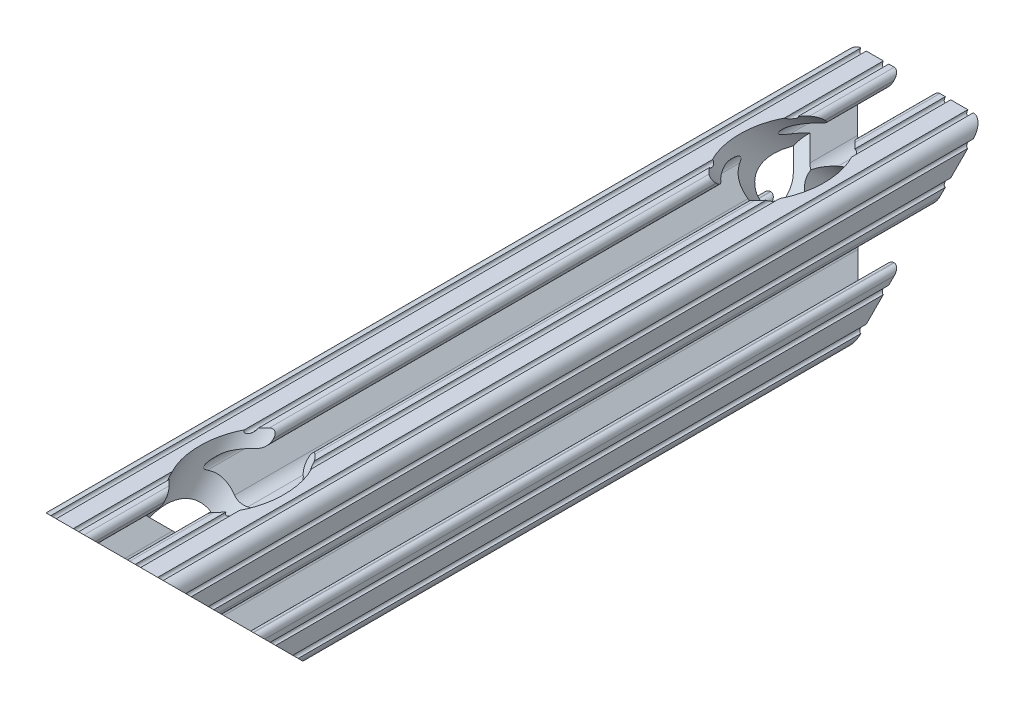
SolidWorks part; units mm, degrees
ref_plane "Front Plane" through (0, 0, 0) normal (0, 0, 1) x (1, 0, 0)
ref_plane "Top Plane" through (0, 0, 0) normal (0, 1, 0) x (1, 0, 0)
ref_plane "Right Plane" through (0, 0, 0) normal (1, 0, 0) x (0, 0, -1)
sketch "Sketch1" plane through (0, 0, 0) normal (0, 0, 1) x (1, 0, 0)
  line L2 (-7.1797, -8.6452) -> (-3.9523, -5.4237)
  line L3 (-1.7093, -4.4958) -> (1.7093, -4.4958)
  line L4 (3.9523, -5.4237) -> (7.1797, -8.6452)
  line L6 (6.4164, -10.4902) -> (4.2875, -10.4902)
  line L7 (3.2385, -11.5392) -> (3.2385, -11.651)
  line L8 (4.2875, -12.7) -> (5.3171, -12.7)
  line L9 (6.3331, -12.7) -> (9.5504, -12.7)
  line L10 (12.7, -9.5504) -> (12.7, -6.3331)
  line L11 (12.7, -5.3171) -> (12.7, -4.2875)
  line L12 (11.651, -3.2385) -> (11.5392, -3.2385)
  line L13 (10.4902, -4.2875) -> (10.4902, -6.4021)
  line L14 (8.7371, -7.1294) -> (5.441, -3.8408)
  line L15 (4.5085, -1.5932) -> (4.5085, 1.5932)
  line L16 (5.441, 3.8408) -> (8.7371, 7.1294)
  line L17 (10.4902, 6.4021) -> (10.4902, 4.2875)
  line L18 (11.5392, 3.2385) -> (11.651, 3.2385)
  line L19 (12.7, 4.2875) -> (12.7, 5.3171)
  line L20 (12.7, 6.3331) -> (12.7, 9.5504)
  line L21 (9.5504, 12.7) -> (6.3331, 12.7)
  line L22 (5.3171, 12.7) -> (4.2875, 12.7)
  line L23 (3.2385, 11.651) -> (3.2385, 11.5392)
  line L24 (4.2875, 10.4902) -> (6.4768, 10.4902)
  line L25 (7.207, 8.7244) -> (3.8983, 5.4232)
  line L26 (1.6558, 4.4958) -> (-1.6558, 4.4958)
  line L27 (-3.8983, 5.4232) -> (-7.207, 8.7244)
  line L28 (-6.4768, 10.4902) -> (-4.2875, 10.4902)
  line L29 (-3.2385, 11.5392) -> (-3.2385, 11.651)
  line L30 (-4.2875, 12.7) -> (-5.3171, 12.7)
  line L31 (-6.3331, 12.7) -> (-9.5504, 12.7)
  line L32 (-12.7, 9.5504) -> (-12.7, 6.3331)
  line L33 (-12.7, 5.3171) -> (-12.7, 4.2875)
  line L34 (-11.651, 3.2385) -> (-11.5392, 3.2385)
  line L35 (-10.4902, 4.2875) -> (-10.4902, 6.4021)
  line L36 (-8.7371, 7.1294) -> (-5.441, 3.8408)
  line L37 (-4.5085, 1.5932) -> (-4.5085, -1.5932)
  line L38 (-5.441, -3.8408) -> (-8.7371, -7.1294)
  line L39 (-10.4902, -6.4021) -> (-10.4902, -4.2875)
  line L40 (-11.5392, -3.2385) -> (-11.651, -3.2385)
  line L41 (-12.7, -4.2875) -> (-12.7, -5.3171)
  line L42 (-12.7, -6.3331) -> (-12.7, -9.5504)
  line L43 (-9.5504, -12.7) -> (-6.3331, -12.7)
  line L44 (-5.3171, -12.7) -> (-4.2875, -12.7)
  line L45 (-3.2385, -11.651) -> (-3.2385, -11.5392)
  line L46 (-4.2875, -10.4902) -> (-6.4164, -10.4902)
  circle A0 centre (0, 0) radius 2.6035
  arc A1 (-7.1797, -8.6452) -> (-6.4164, -10.4902) centre (-6.4164, -9.4098) ccw
  arc A2 (-1.7093, -4.4958) -> (-3.9523, -5.4237) centre (-1.7093, -7.6708) ccw
  arc A3 (3.9523, -5.4237) -> (1.7093, -4.4958) centre (1.7093, -7.6708) ccw
  arc A4 (6.4164, -10.4902) -> (7.1797, -8.6452) centre (6.4164, -9.4098) ccw
  arc A5 (4.2875, -10.4902) -> (3.2385, -11.5392) centre (4.2875, -11.5392) ccw
  arc A6 (3.2385, -11.651) -> (4.2875, -12.7) centre (4.2875, -11.651) ccw
  arc A7 (6.3331, -12.7) -> (5.3171, -12.7) centre (5.8251, -12.7) ccw
  arc A8 (10.5664, -12.6998) -> (9.5504, -12.7) centre (10.0584, -12.7) ccw
  arc A9 (10.5664, -12.6998) -> (12.6998, -10.5664) centre (10.5918, -10.5918) ccw
  arc A10 (12.7, -9.5504) -> (12.6998, -10.5664) centre (12.7, -10.0584) ccw
  arc A11 (12.7, -5.3171) -> (12.7, -6.3331) centre (12.7, -5.8251) ccw
  arc A12 (12.7, -4.2875) -> (11.651, -3.2385) centre (11.651, -4.2875) ccw
  arc A13 (11.5392, -3.2385) -> (10.4902, -4.2875) centre (11.5392, -4.2875) ccw
  arc A14 (8.7371, -7.1294) -> (10.4902, -6.4021) centre (9.4628, -6.4021) ccw
  arc A15 (4.5085, -1.5932) -> (5.441, -3.8408) centre (7.6835, -1.5932) ccw
  arc A16 (5.441, 3.8408) -> (4.5085, 1.5932) centre (7.6835, 1.5932) ccw
  arc A17 (10.4902, 6.4021) -> (8.7371, 7.1294) centre (9.4628, 6.4021) ccw
  arc A18 (10.4902, 4.2875) -> (11.5392, 3.2385) centre (11.5392, 4.2875) ccw
  arc A19 (11.651, 3.2385) -> (12.7, 4.2875) centre (11.651, 4.2875) ccw
  arc A20 (12.7, 6.3331) -> (12.7, 5.3171) centre (12.7, 5.8251) ccw
  arc A21 (12.6998, 10.5664) -> (12.7, 9.5504) centre (12.7, 10.0584) ccw
  arc A22 (12.6998, 10.5664) -> (10.5664, 12.6998) centre (10.5918, 10.5918) ccw
  arc A23 (9.5504, 12.7) -> (10.5664, 12.6998) centre (10.0584, 12.7) ccw
  arc A24 (5.3171, 12.7) -> (6.3331, 12.7) centre (5.8251, 12.7) ccw
  arc A25 (4.2875, 12.7) -> (3.2385, 11.651) centre (4.2875, 11.651) ccw
  arc A26 (3.2385, 11.5392) -> (4.2875, 10.4902) centre (4.2875, 11.5392) ccw
  arc A27 (7.207, 8.7244) -> (6.4768, 10.4902) centre (6.4768, 9.4563) ccw
  arc A28 (1.6558, 4.4958) -> (3.8983, 5.4232) centre (1.6558, 7.6708) ccw
  arc A29 (-3.8983, 5.4232) -> (-1.6558, 4.4958) centre (-1.6558, 7.6708) ccw
  arc A30 (-6.4768, 10.4902) -> (-7.207, 8.7244) centre (-6.4768, 9.4563) ccw
  arc A31 (-4.2875, 10.4902) -> (-3.2385, 11.5392) centre (-4.2875, 11.5392) ccw
  arc A32 (-3.2385, 11.651) -> (-4.2875, 12.7) centre (-4.2875, 11.651) ccw
  arc A33 (-6.3331, 12.7) -> (-5.3171, 12.7) centre (-5.8251, 12.7) ccw
  arc A34 (-10.5664, 12.6998) -> (-9.5504, 12.7) centre (-10.0584, 12.7) ccw
  arc A35 (-10.5664, 12.6998) -> (-12.6998, 10.5664) centre (-10.5918, 10.5918) ccw
  arc A36 (-12.7, 9.5504) -> (-12.6998, 10.5664) centre (-12.7, 10.0584) ccw
  arc A37 (-12.7, 5.3171) -> (-12.7, 6.3331) centre (-12.7, 5.8251) ccw
  arc A38 (-12.7, 4.2875) -> (-11.651, 3.2385) centre (-11.651, 4.2875) ccw
  arc A39 (-11.5392, 3.2385) -> (-10.4902, 4.2875) centre (-11.5392, 4.2875) ccw
  arc A40 (-8.7371, 7.1294) -> (-10.4902, 6.4021) centre (-9.4628, 6.4021) ccw
  arc A41 (-4.5085, 1.5932) -> (-5.441, 3.8408) centre (-7.6835, 1.5932) ccw
  arc A42 (-5.441, -3.8408) -> (-4.5085, -1.5932) centre (-7.6835, -1.5932) ccw
  arc A43 (-10.4902, -6.4021) -> (-8.7371, -7.1294) centre (-9.4628, -6.4021) ccw
  arc A44 (-10.4902, -4.2875) -> (-11.5392, -3.2385) centre (-11.5392, -4.2875) ccw
  arc A45 (-11.651, -3.2385) -> (-12.7, -4.2875) centre (-11.651, -4.2875) ccw
  arc A46 (-12.7, -6.3331) -> (-12.7, -5.3171) centre (-12.7, -5.8251) ccw
  arc A47 (-12.6998, -10.5664) -> (-12.7, -9.5504) centre (-12.7, -10.0584) ccw
  arc A48 (-12.6998, -10.5664) -> (-10.5664, -12.6998) centre (-10.5918, -10.5918) ccw
  arc A49 (-9.5504, -12.7) -> (-10.5664, -12.6998) centre (-10.0584, -12.7) ccw
  arc A50 (-5.3171, -12.7) -> (-6.3331, -12.7) centre (-5.8251, -12.7) ccw
  arc A51 (-4.2875, -12.7) -> (-3.2385, -11.651) centre (-4.2875, -11.651) ccw
  arc A52 (-3.2385, -11.5392) -> (-4.2875, -10.4902) centre (-4.2875, -11.5392) ccw
extrude "Boss-Extrude1" add sketch "Sketch1" along normal mid plane 152.4
sketch "Sketch2" plane through (0, 0, 0) normal (1, 0, 0) x (0, 0, -1)
  line L0 (-76.2, 12.6998) -> (-76.2, -12.7)
  line L1 (-76.2, -12.7) -> (-50.8002, -12.7)
  line L2 (-50.8002, -12.7) -> (-76.2, 12.6998)
  line L3 (0, 0) -> (0, -12.7) construction
  line L5 (50.8002, -12.7) -> (76.2, 12.6998)
  line L6 (76.2, -12.7) -> (50.8002, -12.7)
  line L7 (76.2, 12.6998) -> (76.2, -12.7)
  line L8 (-76.2, -12.7) -> (76.2, -12.7) construction
extrude "Cut-Extrude1" cut sketch "Sketch2" against normal through all and the other way through all
sketch "Sketch3" plane through (0, 0, 0) normal (1, 0, 0) x (0, 0, -1)
  line L0 (-45.1876, 18.3125) -> (-63.5002, 0)
  line L1 (-63.5002, 0) -> (-65.8081, 2.3079)
  line L2 (-65.8081, 2.3079) -> (-61.318, 6.7981)
  line L3 (-61.318, 6.7981) -> (-64.6227, 10.1028)
  line L4 (-64.6227, 10.1028) -> (-50.8003, 23.9252)
  line L5 (-50.8003, 23.9252) -> (-45.1876, 18.3125)
  line L6 (-63.5002, 0) -> (-65.8081, -2.3079) construction
  line L7 (-50.8002, -12.7) -> (-76.2, 12.6998) construction
  line L8 (-66.1037, 2.6035) -> (-60.8967, -2.6035) construction
  line L9 (-53.3974, -1.1225) -> (-39.575, 12.6998) construction
  dimension "D1" = 6.5278
  dimension "D2" = 15.875
  dimension "D3" = 6.35
revolve "Cut-Revolve1" cut sketch "Sketch3" angle 360 about L6
mirror "Mirror1" about plane through (0, 0, 0) normal (0, 0, 1) of "Cut-Revolve1"
